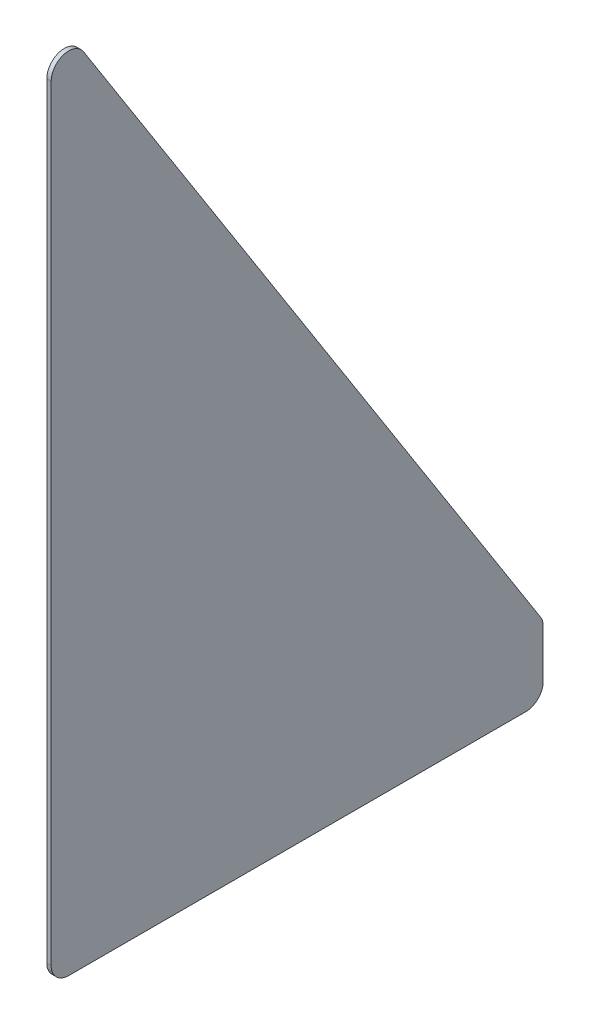
SolidWorks part; units mm, degrees
material "PC High Viscosity"
ref_plane "Front Plane" through (0, 0, 0) normal (0, 0, 1) x (1, 0, 0)
ref_plane "Top Plane" through (0, 0, 0) normal (0, 1, 0) x (1, 0, 0)
ref_plane "Right Plane" through (0, 0, 0) normal (1, 0, 0) x (0, 0, -1)
sketch "Sketch1" plane through (0, 0, 0) normal (0, 1, 0) x (1, 0, 0)
  line L0 (0, 0) -> (0, 177.8)
  line L1 (0, 177.8) -> (1.5875, 177.8)
  line L2 (1.5875, 177.8) -> (1.5875, 0)
  line L5 (1.5875, 0) -> (0, 0)
  point P3 (0, 0)
  dimension "D2" = 177.8
  dimension "D4" = 1.5875
extrude "Boss-Extrude1" add sketch "Sketch1" along normal blind 304.8
sketch "Sketch2" plane through (0, 0, 0) normal (-1, 0, 0) x (0, 0, 1)
  line L0 (-177.8, 25.4) -> (0, 304.8)
  line L1 (0, 304.8) -> (-177.8, 304.8)
  line L2 (-177.8, 304.8) -> (-177.8, 25.4)
  line L4 (-177.8, 304.8) -> (-177.8, 0) construction
  line L5 (-177.8, 304.8) -> (0, 304.8) construction
  line L6 (0, 304.8) -> (0, 0) construction
  dimension "D2" = 25.4
extrude "Cut-Extrude1" cut sketch "Sketch2" against normal up to surface (1.5875 mm away) up to face at (1.5875, 152.4, -88.9)
fillet "Fillet1" radius 6.35 4 edges at (0.7938, 0, -177.8) (0.7938, 0, 0) (0.7938, 304.8, 0) (0.7937, 25.4, -177.8)
